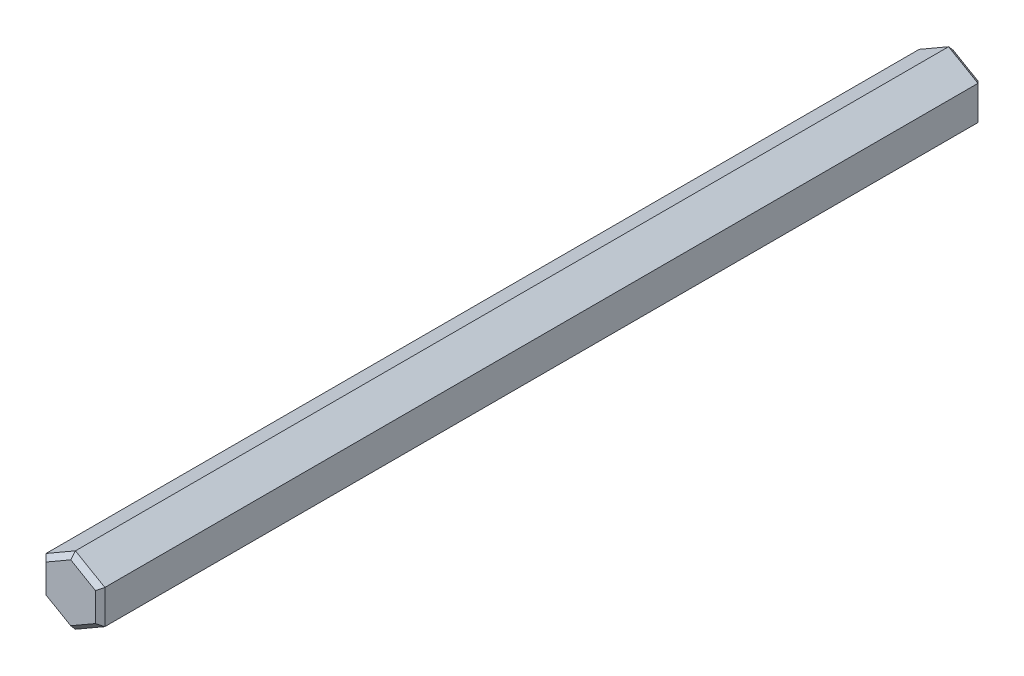
SolidWorks part; units mm, degrees
material "Plain Carbon Steel"
ref_plane "Front Plane" through (0, 0, 0) normal (0, 0, 1) x (1, 0, 0)
ref_plane "Top Plane" through (0, 0, 0) normal (0, 1, 0) x (1, 0, 0)
ref_plane "Right Plane" through (0, 0, 0) normal (1, 0, 0) x (0, 0, -1)
ref_plane "Plane1" through (0, 0, 75) normal (0, 0, 1) x (1, 0, 0)
sketch "Sketch1" plane through (0, 0, 75) normal (0, 0, 1) x (1, 0, 0)
  line L0 (0, -2.8868) -> (2.5, -1.4434)
  line L1 (2.5, -1.4434) -> (2.5, 1.4434)
  line L2 (2.5, 1.4434) -> (0, 2.8868)
  line L3 (0, 2.8868) -> (-2.5, 1.4434)
  line L4 (-2.5, 1.4434) -> (-2.5, -1.4434)
  line L5 (-2.5, -1.4434) -> (0, -2.8868)
extrude "Boss-Extrude1" add sketch "Sketch1" against normal blind 75
chamfer "Chamfer1" distance 0.4 angle 45 12 edges at (-2.5, 0, 0) (-1.25, -2.1651, 0) (-1.25, 2.1651, 0) (1.25, -2.1651, 0) (1.25, 2.1651, 0) (2.5, 0, 0) (-1.25, 2.1651, 75) (-2.5, 0, 75) (1.25, 2.1651, 75) (-1.25, -2.1651, 75) (2.5, 0, 75) (1.25, -2.1651, 75)
